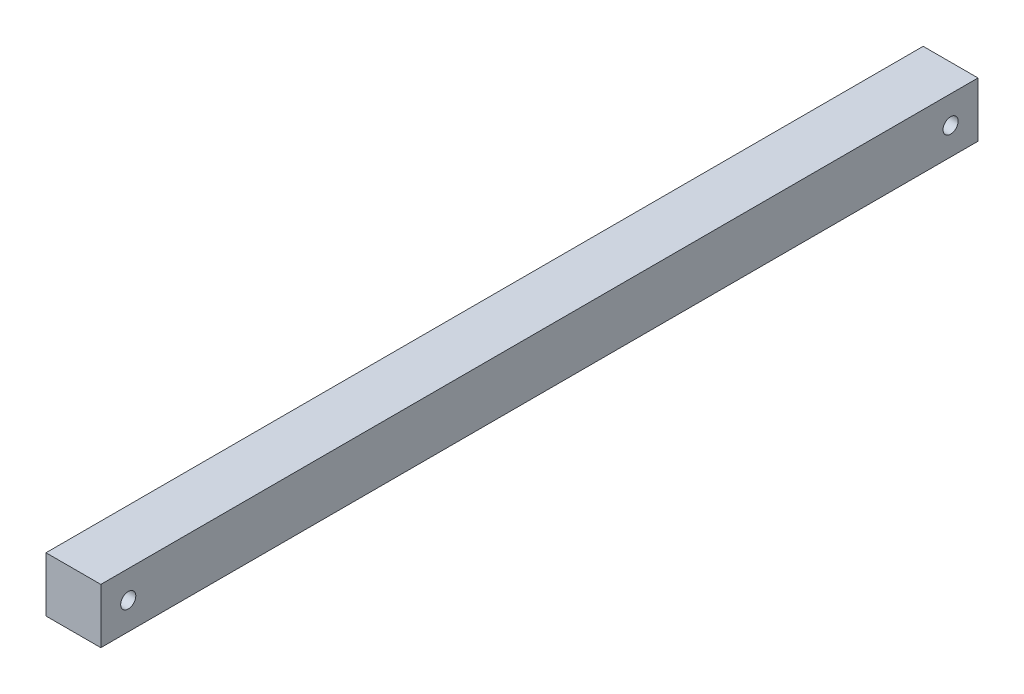
SolidWorks part; units mm, degrees
ref_plane "Front Plane" through (0, 0, 0) normal (0, 0, 1) x (1, 0, 0)
ref_plane "Top Plane" through (0, 0, 0) normal (0, 1, 0) x (1, 0, 0)
ref_plane "Right Plane" through (0, 0, 0) normal (1, 0, 0) x (0, 0, -1)
sketch "Sketch1" plane through (0, 0, 0) normal (0, 0, 1) x (1, 0, 0)
  line L5 (-12.7, -12.7) -> (12.7, -12.7)
  line L6 (-12.7, -12.7) -> (-12.7, 12.7)
  line L7 (-12.7, 12.7) -> (12.7, 12.7)
  line L8 (12.7, -12.7) -> (12.7, 12.7)
  line L9 (-12.7, -12.7) -> (12.7, 12.7) construction
  line L10 (-12.7, 12.7) -> (12.7, -12.7) construction
  point P0 (0, 0)
  dimension "D1" = 25.4
  dimension "D2" = 25.4
extrude "Boss-Extrude1" add sketch "Sketch1" along normal blind 406.4
sketch "Sketch10" plane through (-12.7, 0, 0) normal (-1, 0, 0) x (0, 0, 1)
  line L0 (203.2, 12.7) -> (203.2, 75.2381) construction
  line L1 (406.4, 12.7) -> (0, 12.7) construction
  line L2 (406.4, 12.7) -> (406.4, -12.7) construction
  circle A0 centre (393.7, 0) radius 3.5
  circle A1 centre (12.7, 0) radius 3.5
  dimension "D1" = 7
  dimension "D3" = 12.7
  dimension "D2" = 12.7
extrude "Cut-Extrude6" cut sketch "Sketch10" against normal through all
